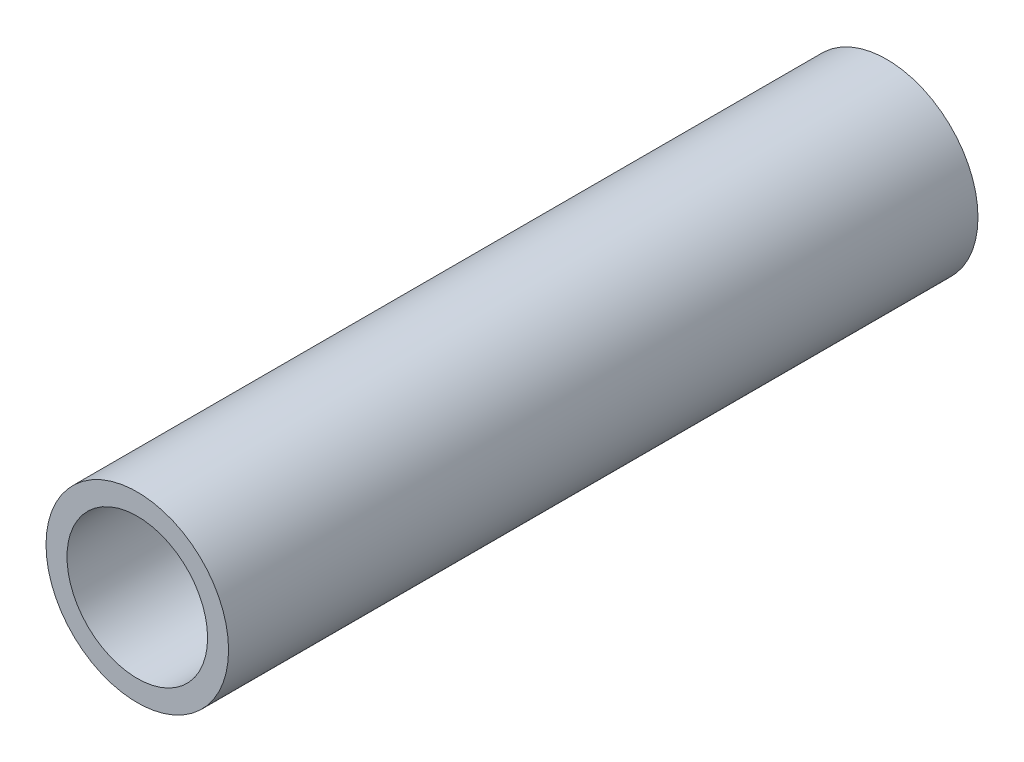
SolidWorks part; units mm, degrees
material "1.0045 (S355JR)"
ref_plane "Front Plane" through (0, 0, 0) normal (0, 0, 1) x (1, 0, 0)
ref_plane "Top Plane" through (0, 0, 0) normal (0, 1, 0) x (1, 0, 0)
ref_plane "Right Plane" through (0, 0, 0) normal (1, 0, 0) x (0, 0, -1)
sketch "Sketch1" plane through (0, 0, 0) normal (0, 0, 1) x (1, 0, 0)
  circle A0 centre (0, 0) radius 30.4515
  circle A1 centre (0, 0) radius 23.4515
extrude "Boss-Extrude1" add sketch "Sketch1" along normal blind 250
